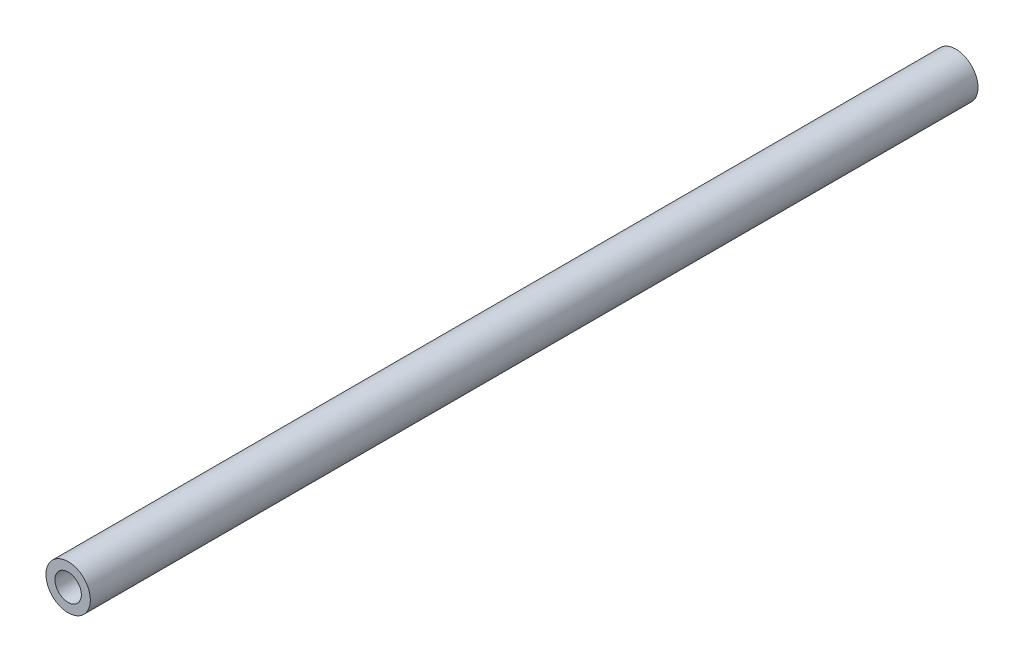
SolidWorks part; units mm, degrees
ref_plane "Front Plane" through (0, 0, 0) normal (0, 0, 1) x (1, 0, 0)
ref_plane "Top Plane" through (0, 0, 0) normal (0, 1, 0) x (1, 0, 0)
ref_plane "Right Plane" through (0, 0, 0) normal (1, 0, 0) x (0, 0, -1)
sketch "Sketch1" plane through (0, 0, 0) normal (0, 0, 1) x (1, 0, 0)
  circle A0 centre (0, 0) radius 8
  dimension "D1" = 16
extrude "Boss-Extrude1" add sketch "Sketch1" along normal blind 320
sketch "Sketch2" plane through (0, 0, 0) normal (0, 0, -1) x (-1, 0, 0)
  circle A0 centre (0, 0) radius 4.755
  dimension "D1" = 9.51
extrude "Cut-Extrude1" cut sketch "Sketch2" against normal through all
